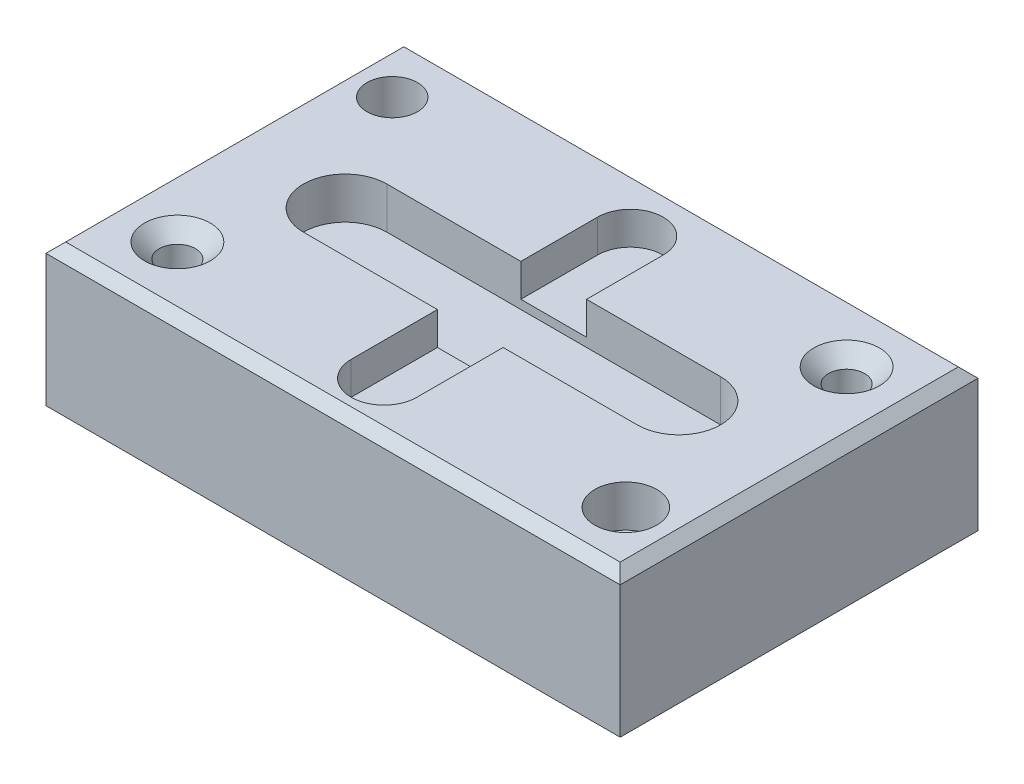
SolidWorks part; units mm, degrees
ref_plane "Front Plane" through (0, 0, 0) normal (0, 0, 1) x (1, 0, 0)
ref_plane "Top Plane" through (0, 0, 0) normal (0, 1, 0) x (1, 0, 0)
ref_plane "Right Plane" through (0, 0, 0) normal (1, 0, 0) x (0, 0, -1)
sketch "Sketch1" plane through (0, 0, 0) normal (0, 1, 0) x (1, 0, 0)
  line L1 (-87.3981, -54.4636) -> (87.3981, -54.4636)
  line L2 (-87.3981, -54.4636) -> (-87.3981, 54.4636)
  line L3 (-87.3981, 54.4636) -> (87.3981, 54.4636)
  line L4 (87.3981, -54.4636) -> (87.3981, 54.4636)
  line L5 (-87.3981, -54.4636) -> (87.3981, 54.4636) construction
  line L6 (-87.3981, 54.4636) -> (87.3981, -54.4636) construction
  point P0 (0, 0)
extrude "Boss-Extrude1" add sketch "Sketch1" along normal blind 43.18
sketch "Sketch2" plane through (0, 43.18, 0) normal (0, 1, 0) x (1, 0, 0)
  line L0 (-50.8, 0) -> (50.8, 0) construction
  line L1 (-50.8, 12.7) -> (50.8, 12.7)
  line L2 (-50.8, -12.7) -> (50.8, -12.7)
  arc A0 (-50.8, 12.7) -> (-50.8, -12.7) centre (-50.8, 0) ccw
  arc A1 (50.8, -12.7) -> (50.8, 12.7) centre (50.8, 0) ccw
  circle A2 centre (-72.874, 36.4086) radius 7.6974
  circle A3 centre (70.8013, -36.1578) radius 9.4308
  point P2 (0, 0)
  dimension "D2" = 101.6
  dimension "D1" = 25.4
extrude "Cut-Extrude1" cut sketch "Sketch2" against normal blind 12.7
sketch "Sketch3" plane through (0, 43.18, 0) normal (0, 1, 0) x (1, 0, 0)
  line L0 (0, 36.0364) -> (0, -38.9636) construction
  line L1 (10, 36.0364) -> (10, -38.9636)
  line L2 (-10, 36.0364) -> (-10, -38.9636)
  line L6 (-87.3981, -54.4636) -> (87.3981, -54.4636) construction
  arc A0 (10, 36.0364) -> (-10, 36.0364) centre (0, 36.0364) ccw
  arc A1 (-10, -38.9636) -> (10, -38.9636) centre (0, -38.9636) ccw
  point P3 (0, -1.4636)
  point P8 (0, 0)
  point P11 (0, 0)
  dimension "D1" = 10
  dimension "D3" = 53
  dimension "D2" = 75
extrude "Cut-Extrude2" cut sketch "Sketch3" against normal blind 10
hole_wizard "CSK for M10 Flat Head Machine Screw1" positions "Sketch4" profile "Sketch5" countersink size "M10" standard "ANSI Metric"
sketch "Sketch4" plane through (0, 43.18, 0) normal (0, 1, 0) x (1, 0, 0)
  line L0 (-87.3981, 54.4636) -> (-87.3981, -54.4636) construction
  line L1 (-87.3981, -54.4636) -> (87.3981, -54.4636) construction
  line L2 (87.3981, -54.4636) -> (87.3981, 54.4636) construction
  line L3 (87.3981, 54.4636) -> (-87.3981, 54.4636) construction
  point P0 (67.3981, 34.4636)
  point P2 (-67.3981, -34.4636)
  dimension "D1" = 20
  dimension "D2" = 20
  dimension "D3" = 20
  dimension "D4" = 20
sketch "Sketch5" plane through (67.3981, 43.18, -34.4636) normal (1, 0, 0) x (0, 0, 1)
  line L0 (0, 0) -> (0, 20)
  line L1 (0, 20) -> (5.5, 16.6953)
  line L2 (5.5, 16.6953) -> (5.5, 4.5)
  line L3 (5.5, 4.5) -> (10, 0)
  line L5 (10, 0) -> (0, 0)
  line L6 (-5.5, 4.5) -> (-10, 0) construction
  line L10 (0, 20) -> (-5.5, 16.6953) construction
  line L11 (0, -6.35) -> (0, 107.95) construction
  dimension "Hole Dia." = 11
  dimension "Hole Depth" = 20
  dimension "Near C'Sink Dia." = 20
  dimension "Near C'Sink Angle" = 90
  dimension "Drill Angle" = 118
chamfer "Chamfer1" distance 3 angle 45 4 edges at (-87.3981, 43.18, 0) (0, 43.18, 54.4636) (87.3981, 43.18, 0) (0, 43.18, -54.4636)
